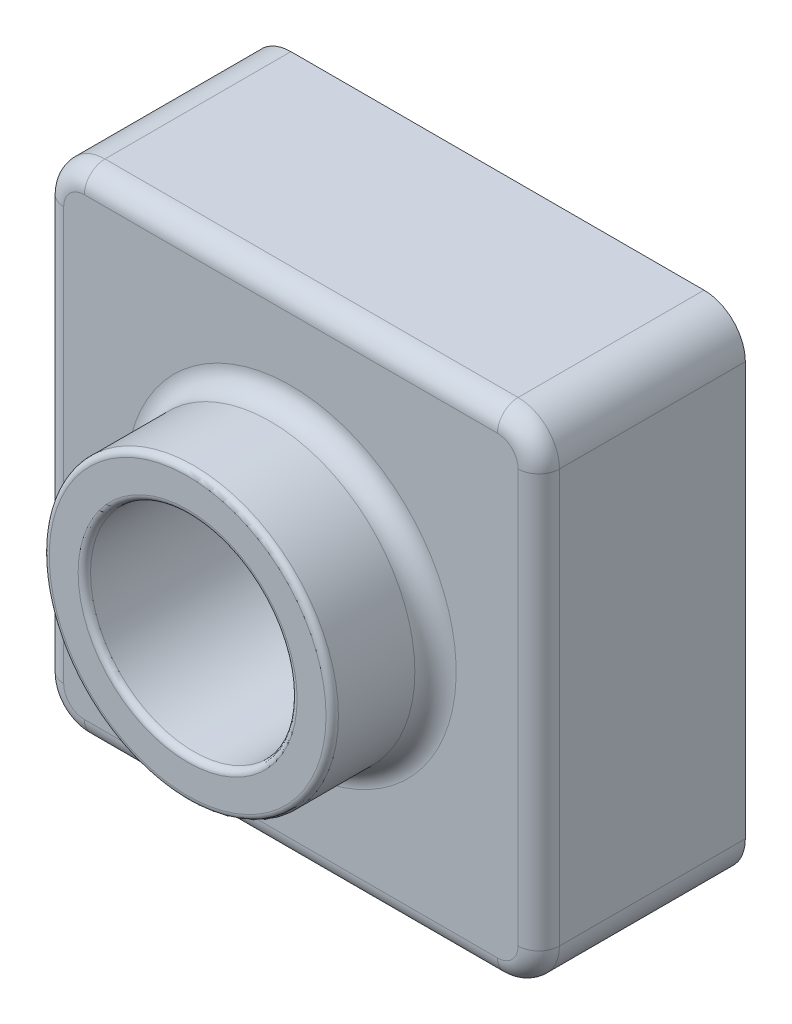
SolidWorks part; units mm, degrees
ref_plane "Front" through (0, 0, 0) normal (0, 0, 1) x (1, 0, 0)
ref_plane "Top" through (0, 0, 0) normal (0, 1, 0) x (1, 0, 0)
ref_plane "Right" through (0, 0, 0) normal (1, 0, 0) x (0, 0, -1)
sketch "Sketch1" plane through (0, 0, 0) normal (0, 0, 1) x (1, 0, 0)
  line L1 (0, 0) -> (120, 0)
  line L2 (0, 0) -> (0, 120)
  line L3 (0, 120) -> (120, 120)
  line L4 (120, 0) -> (120, 120)
  dimension "D1" = 120
  dimension "D2" = 120
extrude "Boss-Extrude1" add sketch "Sketch1" along normal blind 50
sketch "Sketch2" plane through (0, 0, 50) normal (0, 0, 1) x (1, 0, 0)
  line L0 (120, 120) -> (0, 120) construction
  line L1 (120, 0) -> (120, 120) construction
  circle A0 centre (60, 60) radius 35
  dimension "D1" = 70
  dimension "D2" = 60
  dimension "D3" = 60
extrude "Boss-Extrude2" add sketch "Sketch2" along normal blind 25
sketch "Sketch3" plane through (0, 0, 75) normal (0, 0, 1) x (1, 0, 0)
  circle A0 centre (60, 60) radius 25
  dimension "D1" = 50
extrude "Cut-Extrude1" cut sketch "Sketch3" against normal through all
fillet "Fillet1" radius 10 4 edges at (0, 0, 25) (120, 0, 25) (0, 120, 25) (120, 120, 25)
fillet "Fillet2" radius 1.5 2 edges at (95, 60, 75) (85, 60, 75)
fillet "Fillet3" radius 5 9 edges at (25, 60, 50) (2.9289, 117.0711, 50) (60, 120, 50) (117.0711, 117.0711, 50) (120, 60, 50) (117.0711, 2.9289, 50) (60, 0, 50) (2.9289, 2.9289, 50) (0, 60, 50)
shell "Shell1" thickness 2
